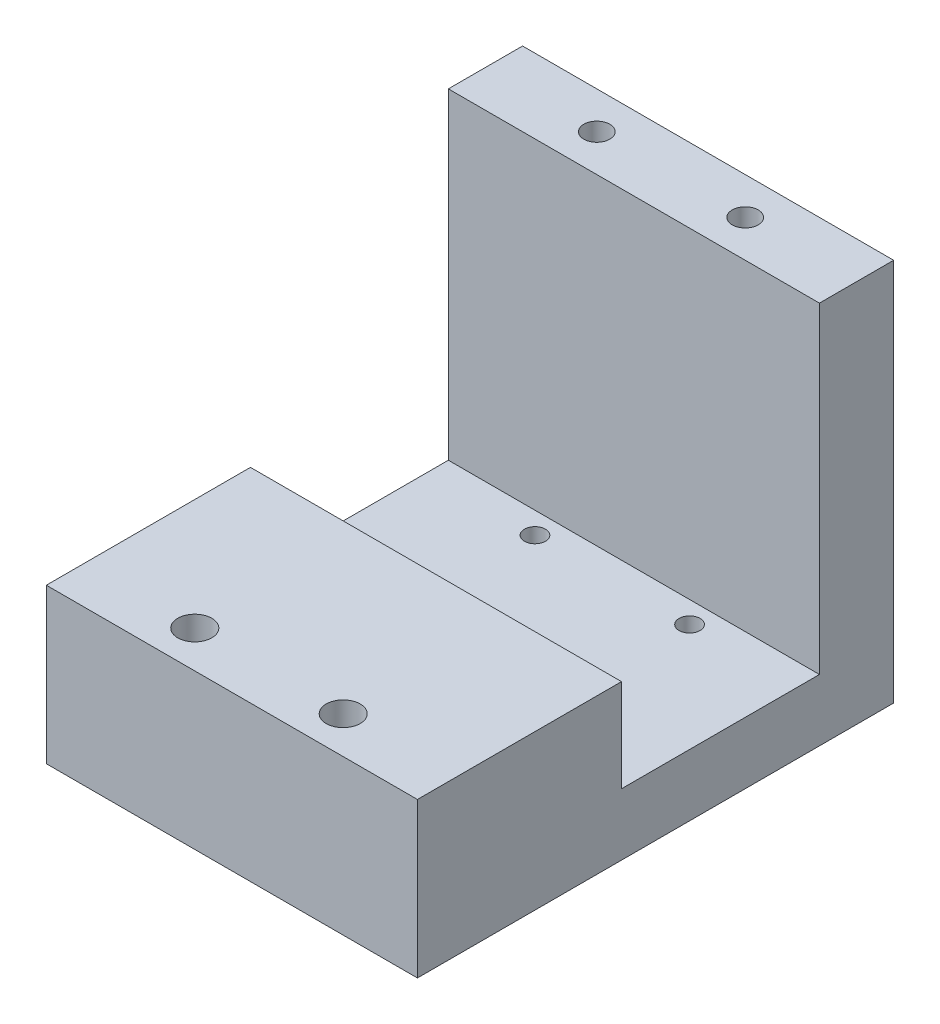
SolidWorks part; units mm, degrees
ref_plane "Front Plane" through (0, 0, 0) normal (0, 0, 1) x (1, 0, 0)
ref_plane "Top Plane" through (0, 0, 0) normal (0, 1, 0) x (1, 0, 0)
ref_plane "Right Plane" through (0, 0, 0) normal (1, 0, 0) x (0, 0, -1)
sketch "Sketch1" plane through (0, 0, 0) normal (0, 1, 0) x (1, 0, 0)
  line L1 (0, 0) -> (60, 0)
  line L2 (0, 0) -> (0, 77)
  line L3 (0, 77) -> (60, 77)
  line L4 (60, 0) -> (60, 77)
  dimension "D1" = 60
  dimension "D2" = 77
extrude "Boss-Extrude1" add sketch "Sketch1" along normal blind 10
sketch "Sketch2" plane through (0, 10, 0) normal (0, 1, 0) x (1, 0, 0)
  line L0 (60, 0) -> (60, 77) construction
  line L1 (0, 77) -> (60, 77)
  line L2 (0, 77) -> (0, 65)
  line L3 (0, 65) -> (60, 65)
  line L4 (60, 77) -> (60, 65)
  dimension "D1" = 12
extrude "Boss-Extrude2" add sketch "Sketch2" along normal blind 52
sketch "Sketch3" plane through (0, 10, 0) normal (0, 1, 0) x (1, 0, 0)
  line L0 (60, 0) -> (60, 65) construction
  line L1 (0, 0) -> (60, 0)
  line L2 (0, 0) -> (0, 33)
  line L3 (0, 33) -> (60, 33)
  line L4 (60, 0) -> (60, 33)
  dimension "D1" = 33
extrude "Boss-Extrude3" add sketch "Sketch3" along normal blind 15
hole_wizard "M5x0.8 Tapped Hole1" positions "Sketch4" profile "Sketch5" tap size "M5x0.8" standard "ANSI Metric" end condition through all
sketch "Sketch4" plane through (0, 62, 0) normal (0, 1, 0) x (1, 0, 0)
  point P0 (18, 71)
  point P2 (42, 71)
  point P5 (0, 0)
  point P6 (0, 0)
  point P8 (0, 0)
sketch "Sketch5" plane through (18, 62, -71) normal (1, 0, 0) x (0, 0, 1)
  line L0 (0, 0) -> (0, 62)
  line L1 (0, 62) -> (2.1, 62)
  line L2 (2.1, 62) -> (2.1, 0)
  line L5 (2.1, 0) -> (0, 0)
  line L11 (0, -6.35) -> (0, 107.95) construction
  dimension "Thru Tap Drill Dia." = 4.2
  dimension "Thru Tap Drill Depth" = 62
cosmetic thread "Hole Thread1" parameters "D2"=5
cosmetic thread "Hole Thread2" parameters "D2"=5
hole_wizard "CBORE for M5 SHCS1" positions "Sketch6" profile "Sketch7" counterbore size "M5" standard "ANSI Metric" end condition through all
sketch "Sketch6" plane through (0, 0, 0) normal (0, -1, 0) x (-1, 0, 0)
  point P0 (-42, 6)
  point P2 (-18, 6)
  point P6 (0, 0)
  point P8 (0, 0)
sketch "Sketch7" plane through (42, 0, -6) normal (1, 0, 0) x (0, 0, -1)
  line L0 (0, 0) -> (0, 62)
  line L1 (0, 62) -> (2.75, 62)
  line L3 (2.75, 62) -> (2.75, 20)
  line L4 (2.75, 20) -> (5, 20)
  line L5 (5, 20) -> (5, 0)
  line L7 (5, 0) -> (0, 0)
  line L11 (0, -6.35) -> (0, 107.95) construction
  dimension "Thru Hole Dia." = 5.5
  dimension "Thru Hole Depth" = 62
  dimension "C'Bore Dia." = 10
  dimension "C'Bore Depth" = 20
hole_wizard "CBORE for M3 SHCS1" positions "Sketch8" profile "Sketch9" counterbore size "M3" standard "ANSI Metric" end condition through all
sketch "Sketch8" plane through (0, 0, 0) normal (0, -1, 0) x (-1, 0, 0)
  circle A0 centre (-42.5, 36.5) radius 3.25 construction
  circle A1 centre (-42.5, 61.5) radius 3.25 construction
  circle A2 centre (-17.5, 61.5) radius 3.25 construction
  circle A3 centre (-17.5, 36.5) radius 3.25 construction
  point P0 (-42.5, 61.5)
  point P2 (-17.5, 61.5)
  point P4 (-17.5, 36.5)
  point P6 (-42.5, 36.5)
  point P9 (0, 0)
  point P12 (0, 0)
  point P15 (0, 0)
  point P18 (0, 0)
sketch "Sketch9" plane through (42.5, 0, -61.5) normal (1, 0, 0) x (0, 0, -1)
  line L0 (0, 0) -> (0, 62)
  line L1 (0, 62) -> (1.7, 62)
  line L3 (1.7, 62) -> (1.7, 3)
  line L4 (1.7, 3) -> (3.25, 3)
  line L5 (3.25, 3) -> (3.25, 0)
  line L7 (3.25, 0) -> (0, 0)
  line L11 (0, -6.35) -> (0, 107.95) construction
  dimension "Thru Hole Dia." = 3.4
  dimension "Thru Hole Depth" = 62
  dimension "C'Bore Dia." = 6.5
  dimension "C'Bore Depth" = 3
